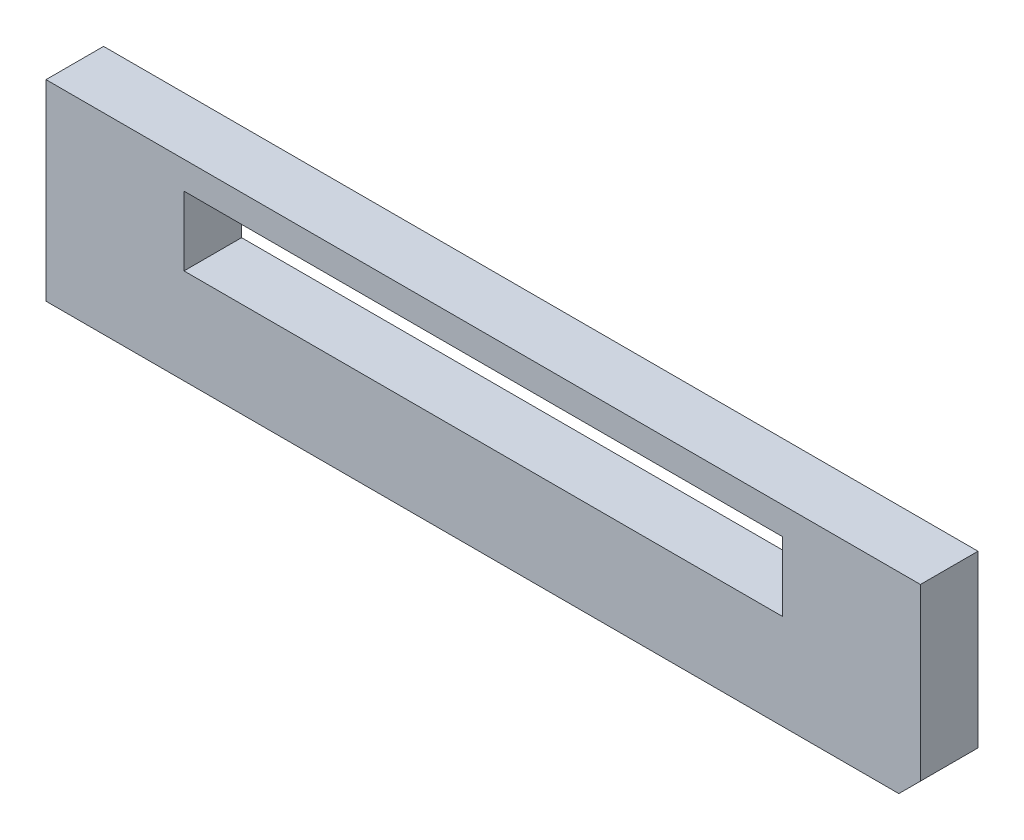
SolidWorks part; units mm, degrees
ref_plane "Спереди" through (0, 0, 0) normal (0, 0, 1) x (1, 0, 0)
ref_plane "Сверху" through (0, 0, 0) normal (0, 1, 0) x (1, 0, 0)
ref_plane "Справа" through (0, 0, 0) normal (1, 0, 0) x (0, 0, -1)
sketch "Эскиз1" plane through (0, 0, 0) normal (0, 0, 1) x (1, 0, 0)
  line L1 (0, 0) -> (81.1, 0)
  line L2 (0, 0) -> (0, 17.8)
  line L3 (0, 17.8) -> (81.1, 17.8)
  line L4 (81.1, 0) -> (81.1, 17.8)
  dimension "D1" = 17.8
  dimension "D2" = 81.1
extrude "Бобышка-Вытянуть1" add sketch "Эскиз1" along normal blind 5.34
chamfer "Фаска1" distance 2 angle 45 1 edges at (81.1, 0, 2.67)
sketch "Эскиз2" plane through (0, 0, 5.34) normal (0, 0, 1) x (1, 0, 0)
  line L0 (81.1, 2) -> (81.1, 17.8) construction
  line L1 (12.8, 8.8339) -> (68.3, 8.8339)
  line L2 (12.8, 8.8339) -> (12.8, 15.2434)
  line L3 (12.8, 15.2434) -> (68.3, 15.2434)
  line L4 (68.3, 8.8339) -> (68.3, 15.2434)
  line L5 (0, 17.8) -> (0, 0) construction
  dimension "D1" = 12.8
  dimension "D2" = 12.8
extrude "Вырез-Вытянуть1" cut sketch "Эскиз2" along direction (0, 0, -1) on the side against the normal through all
